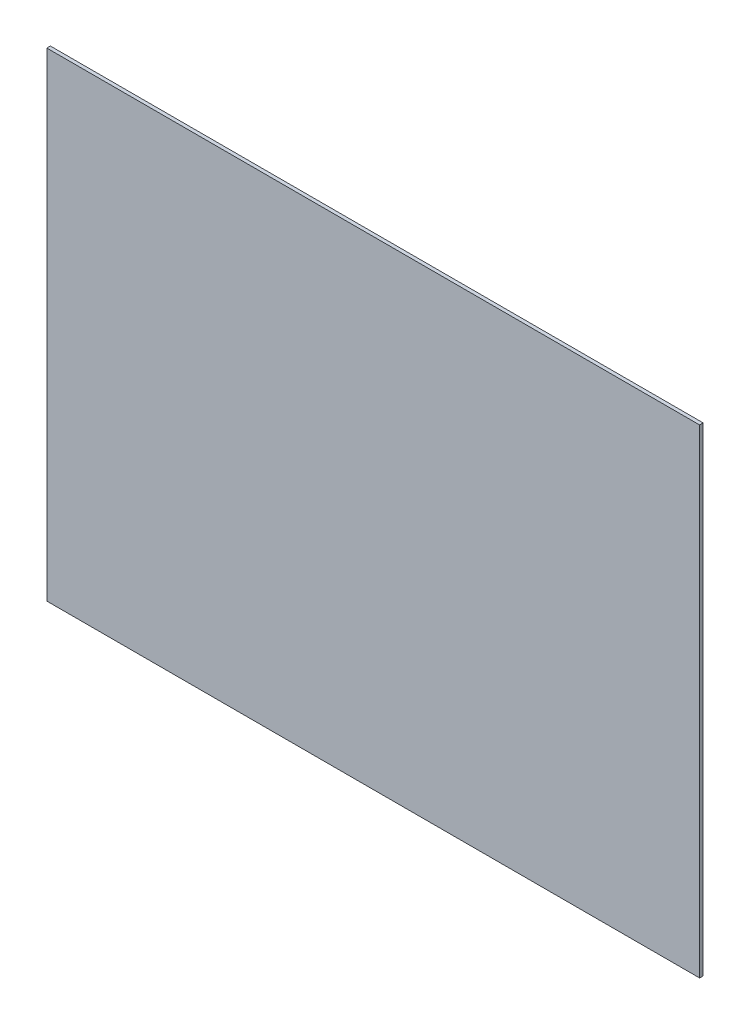
SolidWorks part; units mm, degrees
ref_plane "Front Plane" through (0, 0, 0) normal (0, 0, 1) x (1, 0, 0)
ref_plane "Top Plane" through (0, 0, 0) normal (0, 1, 0) x (1, 0, 0)
ref_plane "Right Plane" through (0, 0, 0) normal (1, 0, 0) x (0, 0, -1)
sketch "Sketch1" plane through (0, 0, 0) normal (0, 0, 1) x (1, 0, 0)
  line L1 (0, 0) -> (584.2, 0)
  line L2 (0, 0) -> (0, 428.625)
  line L3 (0, 428.625) -> (584.2, 428.625)
  line L4 (584.2, 0) -> (584.2, 428.625)
  dimension "D1" = 428.625
  dimension "D2" = 584.2
extrude "Boss-Extrude1" add sketch "Sketch1" along normal blind 3.175
